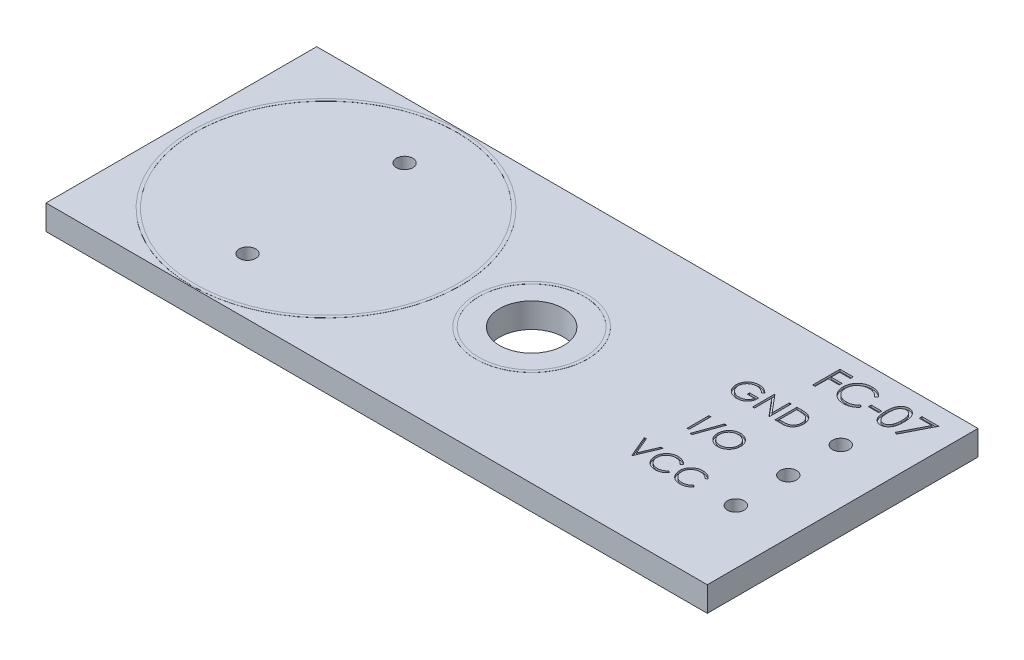
SolidWorks part; units mm, degrees
ref_plane "Front Plane" through (0, 0, 0) normal (0, 0, 1) x (1, 0, 0)
ref_plane "Top Plane" through (0, 0, 0) normal (0, 1, 0) x (1, 0, 0)
ref_plane "Right Plane" through (0, 0, 0) normal (1, 0, 0) x (0, 0, -1)
sketch "Sketch1" plane through (0, 0, 0) normal (0, 1, 0) x (1, 0, 0)
  line L1 (-16, 6.55) -> (16, 6.55)
  line L2 (-16, 6.55) -> (-16, -6.55)
  line L3 (-16, -6.55) -> (16, -6.55)
  line L4 (16, 6.55) -> (16, -6.55)
  line L5 (-16, 6.55) -> (16, -6.55) construction
  line L6 (-16, -6.55) -> (16, 6.55) construction
  point P0 (0, 0)
  dimension "D1" = 13.1
  dimension "D2" = 32
extrude "Boss-Extrude1" add sketch "Sketch1" along normal blind 1.2
sketch "Sketch2" plane through (0, 1.2, 0) normal (0, 1, 0) x (1, 0, 0)
  line L0 (0.95, 0) -> (16, 0) construction
  line L1 (16, -6.55) -> (16, 6.55) construction
  circle A0 centre (0.95, 0) radius 1.55
  dimension "D1" = 3.1
  dimension "D2" = 13.5
extrude "Cut-Extrude1" cut sketch "Sketch2" against normal up to next
sketch "Sketch4" plane through (0, 1.2, 0) normal (0, 1, 0) x (1, 0, 0)
  line L0 (13.37, -2.54) -> (13.37, 0) construction
  line L1 (13.37, 0) -> (13.37, 2.54) construction
  line L2 (13.37, 0) -> (16, 0) construction
  line L3 (16, -6.55) -> (16, 6.55) construction
  circle A0 centre (13.37, 0) radius 0.4
  circle A1 centre (13.37, 2.54) radius 0.4
  circle A2 centre (13.37, -2.54) radius 0.4
  dimension "D1" = 0.8
  dimension "D2" = 2.54
  dimension "D3" = 2.63
extrude "Cut-Extrude2" cut sketch "Sketch4" against normal up to next
sketch "Sketch5" plane through (0, 1.2, 0) normal (0, 1, 0) x (1, 0, 0)
  line L0 (-9, -3.8) -> (-9, 3.8) construction
  line L1 (-9, 0) -> (0, 0) construction
  circle A0 centre (-9, -3.8) radius 0.4
  circle A1 centre (-9, 3.8) radius 0.4
  dimension "D2" = 0.8
  dimension "D1" = 7.6
  dimension "D3" = 9
extrude "Cut-Extrude3" cut sketch "Sketch5" against normal up to next
sketch "Sketch6" plane through (0, 1.2, 0) normal (0, 1, 0) x (1, 0, 0)
  line L0 (7.9604, 1.9986) -> (11.9533, 1.9986) construction
  line L1 (7.9604, -0.4825) -> (11.9533, -0.4825) construction
  line L2 (7.9604, -2.9637) -> (11.9533, -2.9637) construction
  line L3 (9.9568, 1.9986) -> (9.9568, -0.4825) construction
  line L4 (9.9568, -0.4825) -> (9.9568, -2.9637) construction
  text T0 "GND" font "Century Gothic" height in points 4
  text T1 "I/O" font "Century Gothic" height in points 4
  text T2 "VCC" font "Century Gothic" height in points 4
  point P8 (10.3815, 1.6035)
  point P11 (8.785, -0.8949)
  point P12 (8.3365, 1.6224)
  point P13 (10.3764, -0.8659)
  point P14 (10.0292, -0.8804)
  point P15 (7.9604, -0.9383)
  point P16 (10.0581, -2.9637)
  point P17 (9.9568, 1.9986)
extrude "Cut-Extrude4" cut sketch "Sketch6" against normal blind 0.1
sketch "Sketch7" plane through (0, 1.2, 0) normal (0, 1, 0) x (1, 0, 0)
  line L0 (9.6094, 4.3689) -> (15.429, 4.3689) construction
  text T0 "FC-07" font "Century Gothic" height in points 5
extrude "Cut-Extrude5" cut sketch "Sketch7" against normal blind 0.1
sketch "Sketch8" plane through (0, 1.2, 0) normal (0, 1, 0) x (1, 0, 0)
  line L0 (-9, 3.8) -> (-9, 0) construction
  line L1 (-9, 0) -> (-9, -3.8) construction
  circle A0 centre (-9, 0) radius 6.5
  circle A1 centre (-9, 0) radius 6.35
  circle A2 centre (0.95, 0) radius 2.7
  circle A3 centre (0.95, 0) radius 2.55
  dimension "D1" = 13
  dimension "D2" = 0.15
  dimension "D3" = 0.15
  dimension "D4" = 5.4
extrude "Boss-Extrude2" add sketch "Sketch8" along normal blind 0.005
